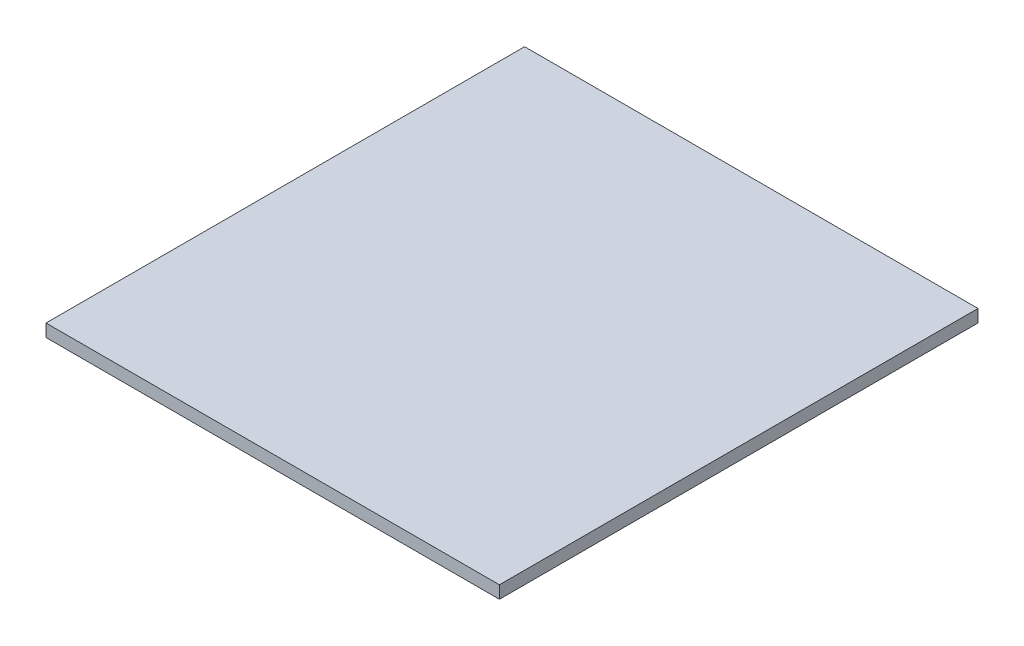
SolidWorks part; units mm, degrees
ref_plane "Front Plane" through (0, 0, 0) normal (0, 0, 1) x (1, 0, 0)
ref_plane "Top Plane" through (0, 0, 0) normal (0, 1, 0) x (1, 0, 0)
ref_plane "Right Plane" through (0, 0, 0) normal (1, 0, 0) x (0, 0, -1)
sketch "Sketch1" plane through (0, 0, 0) normal (0, 1, 0) x (1, 0, 0)
  line L1 (-228.6, -241.3) -> (228.6, -241.3)
  line L2 (-228.6, -241.3) -> (-228.6, 241.3)
  line L3 (-228.6, 241.3) -> (228.6, 241.3)
  line L4 (228.6, -241.3) -> (228.6, 241.3)
  line L5 (-228.6, -241.3) -> (228.6, 241.3) construction
  line L6 (-228.6, 241.3) -> (228.6, -241.3) construction
  point P0 (0, 0)
  dimension "D1" = 457.2
  dimension "D2" = 482.6
extrude "Boss-Extrude1" add sketch "Sketch1" along normal blind 12.7
